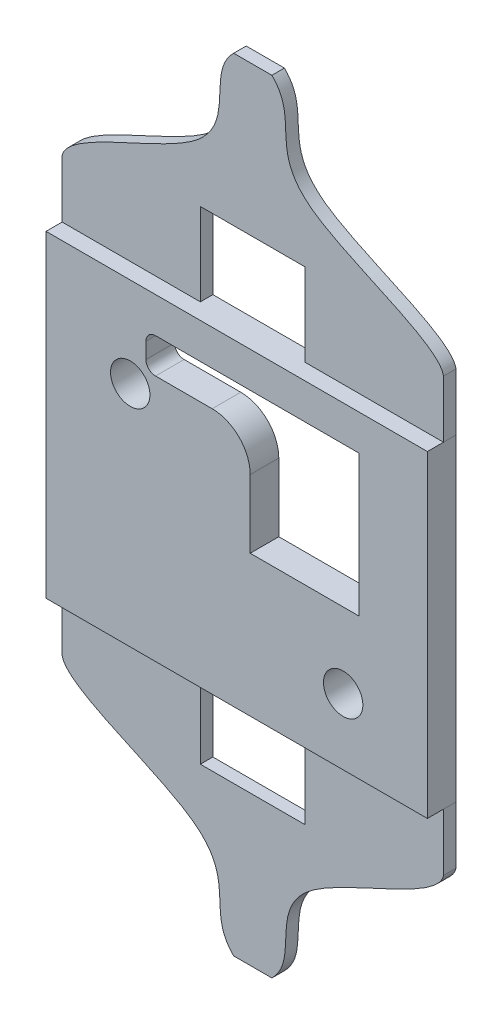
SolidWorks part; units mm, degrees
ref_plane "Front Plane" through (0, 0, 0) normal (0, 0, 1) x (1, 0, 0)
ref_plane "Top Plane" through (0, 0, 0) normal (0, 1, 0) x (1, 0, 0)
ref_plane "Right Plane" through (0, 0, 0) normal (1, 0, 0) x (0, 0, -1)
sketch "Sketch2" plane through (0, 0, 0) normal (0, 0, 1) x (1, 0, 0)
  line L1 (-15.24, -12.7) -> (15.24, -12.7)
  line L2 (-15.24, -12.7) -> (-15.24, 12.7)
  line L3 (-15.24, 12.7) -> (15.24, 12.7)
  line L4 (15.24, -12.7) -> (15.24, 12.7)
  line L5 (-15.24, -12.7) -> (15.24, 12.7) construction
  line L6 (-15.24, 12.7) -> (15.24, -12.7) construction
  point P0 (0, 0)
  dimension "D1" = 25.4
  dimension "D2" = 30.48
extrude "Boss-Extrude1" add sketch "Sketch2" along normal blind 2.286
sketch "Sketch3" plane through (0, 0, 0) normal (0, 0, -1) x (-1, 0, 0)
  line L0 (-1.0795, -1.4224) -> (-1.0795, 7.0358)
  line L1 (-1.0795, 7.0358) -> (-9.7663, 7.0358)
  line L2 (-9.7663, 7.0358) -> (-9.7663, -1.4224)
  line L3 (-9.7663, -1.4224) -> (-1.0795, -1.4224)
  line L4 (-1.4478, -1.0541) -> (-1.4478, 6.6675)
  line L5 (-1.4478, 6.6675) -> (-9.398, 6.6675)
  line L6 (-9.398, 6.6675) -> (-9.398, -1.0541)
  line L7 (-9.398, -1.0541) -> (-1.4478, -1.0541)
  line L8 (-1.4478, -1.0541) -> (-1.4478, 6.6675) construction
  line L9 (-1.4478, 6.6675) -> (-9.398, 6.6675) construction
  line L10 (-9.398, 6.6675) -> (-9.398, -1.0541) construction
  line L11 (-9.398, -1.0541) -> (-1.4478, -1.0541) construction
  line L13 (-9.7663, 7.0358) -> (7.2517, 7.0358)
  line L14 (-9.7663, 7.0358) -> (-9.7663, 9.8552)
  line L15 (-9.7663, 9.8552) -> (7.2517, 9.8552)
  line L16 (7.2517, 7.0358) -> (7.2517, 9.8552)
  line L17 (-1.0795, 7.0358) -> (7.2517, 7.0358)
  line L18 (-1.0795, 7.0358) -> (-1.0795, 7.0612)
  line L19 (-1.0795, 7.0612) -> (7.2517, 7.0612)
  line L20 (7.2517, 7.0358) -> (7.2517, 7.0612)
  circle A0 centre (8.509, 5.5245) radius 1.5748 construction
  circle A1 centre (8.509, 5.5245) radius 1.5748
  circle A2 centre (-8.509, -7.4295) radius 1.5748 construction
  circle A3 centre (-8.509, -7.4295) radius 1.5748
  dimension "D3" = 11.2776
  dimension "D4" = 17.018
  dimension "D2" = 8.4582
  dimension "D5" = 2.794
  dimension "D1" = 0
extrude "Cut-Extrude2" cut sketch "Sketch3" against normal up to next contours L13 L16 L15 L14 L1 | L2 L3 L0 L1 | A3 | A1
sketch "Sketch4" plane through (0, 0, 0) normal (0, 0, -1) x (-1, 0, 0)
  line L0 (-15.24, 12.7) -> (15.24, 12.7) construction
  line L1 (15.24, -12.7) -> (22.733, -12.7)
  line L2 (15.24, -12.7) -> (15.24, 12.7)
  line L3 (15.24, 12.7) -> (22.733, 12.7)
  line L4 (22.733, -12.7) -> (22.733, 12.7)
  line L6 (22.733, 12.7) -> (35.1812, 12.7)
  line L7 (22.733, 12.7) -> (22.733, 7.62)
  line L8 (22.733, 7.62) -> (35.1812, 7.62)
  line L9 (35.1812, 12.7) -> (35.1812, 7.62)
  line L10 (22.733, -12.7) -> (35.1812, -12.7)
  line L11 (22.733, -12.7) -> (22.733, -7.62)
  line L12 (22.733, -7.62) -> (35.1812, -7.62)
  line L13 (35.1812, -12.7) -> (35.1812, -7.62)
  line L14 (35.1812, 12.7) -> (35.4352, 12.7)
  line L15 (35.1812, 12.7) -> (35.1812, 7.62)
  line L16 (35.1812, 7.62) -> (35.4352, 7.62)
  line L17 (35.4352, 12.7) -> (35.4352, 7.62)
  line L18 (35.1812, -7.62) -> (35.4352, -7.62)
  line L19 (35.1812, -7.62) -> (35.1812, -12.7)
  line L20 (35.1812, -12.7) -> (35.4352, -12.7)
  line L21 (35.4352, -7.62) -> (35.4352, -12.7)
  line M19 (15.24, -12.7) -> (15.24, 12.7)
  dimension "D1" = 7.493
  dimension "D2" = 12.4482
  dimension "D3" = 12.4482
  dimension "D4" = 5.08
  dimension "D5" = 5.08
  dimension "D6" = 0.254
  dimension "D7" = 0.254
extrude "Boss-Extrude4" [suppressed] add sketch "Sketch4" against normal blind 1 separate body contours L1 L4 L3 M19 | L9 L6 L4 L8 | L17 L14 L9 L16 | L21 L18 L13 L20 | L10 L13 L12 L4
sketch "Sketch5" plane through (0, 0, 0) normal (0, 0, -1) x (-1, 0, 0)
  line L0 (15.24, 12.7) -> (15.24, -12.7) construction
  line L1 (-15.24, 12.7) -> (15.24, 12.7)
  line L2 (-15.24, 12.7) -> (-15.24, 18.542)
  line L3 (-15.24, 18.542) -> (15.24, 18.542)
  line L4 (15.24, 12.7) -> (15.24, 18.542)
  line L5 (0, 0) -> (5.1341, 0) construction
  line L6 (15.24, -12.7) -> (15.24, -18.542)
  line L7 (-15.24, -18.542) -> (15.24, -18.542)
  line L8 (-15.24, -12.7) -> (-15.24, -18.542)
  line L9 (-15.24, -12.7) -> (15.24, -12.7)
  line L10 (-15.24, 15.621) -> (15.24, 15.621) construction
  line L11 (-4.191, -19.304) -> (4.191, -11.938) construction
  line L12 (-4.191, 11.938) -> (4.191, 11.938)
  line L13 (-4.191, 11.938) -> (-4.191, 19.304)
  line L14 (-4.191, 19.304) -> (4.191, 19.304)
  line L15 (4.191, 11.938) -> (4.191, 19.304)
  line L16 (-4.191, 11.938) -> (4.191, 19.304) construction
  line L17 (-4.191, 19.304) -> (4.191, 11.938) construction
  line L18 (-15.24, 18.542) -> (15.24, 18.542)
  line L19 (-15.24, 18.542) -> (-15.24, 31.242)
  line L20 (-15.24, 31.242) -> (15.24, 31.242)
  line L21 (15.24, 18.542) -> (15.24, 31.242)
  line L22 (-15.24, -18.542) -> (15.24, -18.542)
  line L23 (-4.191, -11.938) -> (4.191, -19.304) construction
  line L24 (-15.24, -15.621) -> (15.24, -15.621) construction
  line L25 (15.24, -18.542) -> (15.24, -31.242)
  line L26 (-15.24, -31.242) -> (15.24, -31.242)
  line L27 (-15.24, -18.542) -> (-15.24, -31.242)
  line L28 (-15.24, -18.542) -> (15.24, -18.542)
  line L29 (4.191, -11.938) -> (4.191, -19.304)
  line L30 (-4.191, -19.304) -> (4.191, -19.304)
  line L31 (-4.191, -11.938) -> (-4.191, -19.304)
  line L32 (-4.191, -11.938) -> (4.191, -11.938)
  line L33 (15.24, -12.7) -> (15.24, -18.542)
  line L34 (-15.24, -18.542) -> (15.24, -18.542)
  line L35 (-15.24, -12.7) -> (-15.24, -18.542)
  line L36 (-15.24, -12.7) -> (15.24, -12.7)
  point P16 (0, 15.621)
  point P31 (0, -15.621)
  line M18 (-15.24, -12.7) -> (15.24, -12.7)
  line M20 (15.24, 12.7) -> (-15.24, 12.7)
  dimension "D1" = 37.084
  dimension "D2" = 8.382
  dimension "D3" = 7.366
  dimension "D4" = 12.7
extrude "Boss-Extrude5" add sketch "Sketch5" against normal blind 1 separate body contours L3 L21 L20 L19 | L7 L27 L26 L25 | L31 L8 L7 M18 | L9 L29 L28 L6 | L15 L4 L3 M20 | L1 L13 L3 L2
sketch "Sketch6" plane through (0, 0, 0) normal (0, 0, -1) x (-1, 0, 0)
  line L2 (15.24, -23.622) -> (-15.24, -23.622) construction
  line L4 (0, 0) -> (0, -8.0809) construction
  line L5 (0, 0) -> (7.6629, 0) construction
  line L6 (15.24, -17.2808) -> (15.24, -31.242)
  line L7 (15.24, -31.242) -> (1.5269, -31.242)
  line L8 (-15.24, -31.242) -> (-1.5269, -31.242)
  line L9 (-15.24, -17.2808) -> (-15.24, -31.242)
  line L10 (15.24, 23.622) -> (-15.24, 23.622) construction
  line L11 (-15.24, 17.2808) -> (-15.24, 31.242)
  line L12 (-15.24, 31.242) -> (-1.5269, 31.242)
  line L13 (15.24, 31.242) -> (1.5269, 31.242)
  line L14 (15.24, 17.2808) -> (15.24, 31.242)
  line L15 (15.24, -12.7) -> (15.24, -31.242) construction
  line L16 (-15.24, -31.242) -> (15.24, -31.242) construction
  spline S0 degree 3 poles (15.24, -17.2808) (14.8904, -19.3097) (-1.0014, -23.8817) (3.7988, -29.0157) (1.5269, -31.242) knots 0 0 0 0 0.45867 1 1 1 1
  spline S1 degree 3 poles (-15.24, -17.2808) (-14.8904, -19.3097) (1.0014, -23.8817) (-3.7988, -29.0157) (-1.5269, -31.242) knots 0 0 0 0 0.45867 1 1 1 1
  spline S2 degree 3 poles (-15.24, 17.2808) (-14.8904, 19.3097) (1.0014, 23.8817) (-3.7988, 29.0157) (-1.5269, 31.242) knots 0 0 0 0 0.45867 1 1 1 1
  spline S3 degree 3 poles (15.24, 17.2808) (14.8904, 19.3097) (-1.0014, 23.8817) (3.7988, 29.0157) (1.5269, 31.242) knots 0 0 0 0 0.45867 1 1 1 1
  dimension "D1" = 7.62
extrude "Cut-Extrude3" cut sketch "Sketch6" against normal up to next (1 mm away)
fillet "Fillet4" radius 3.04 1 edges at (1.0795, 7.0612, 1.143)
fillet "Fillet5" radius 0.762 2 edges at (-7.2517, 9.8552, 1.143) (-7.2517, 7.0612, 1.143)
